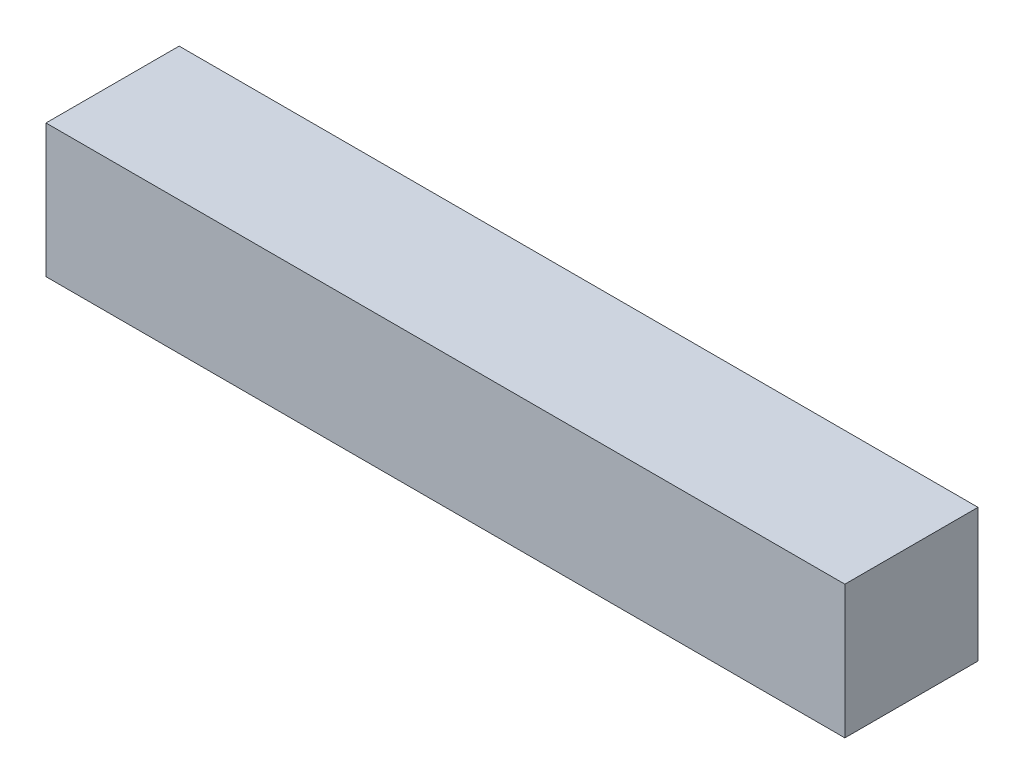
SolidWorks part; units mm, degrees
material "Plain Carbon Steel"
ref_plane "Front" through (0, 0, 0) normal (0, 0, 1) x (1, 0, 0)
ref_plane "Top" through (0, 0, 0) normal (0, 1, 0) x (1, 0, 0)
ref_plane "Right" through (0, 0, 0) normal (1, 0, 0) x (0, 0, -1)
sketch "Sketch1" plane through (0, 0, 0) normal (1, 0, 0) x (0, 0, -1)
  line L1 (0, 0) -> (25.4, 0)
  line L2 (0, 0) -> (0, 25.4)
  line L3 (0, 25.4) -> (25.4, 25.4)
  line L4 (25.4, 0) -> (25.4, 25.4)
  dimension "D1" = 25.4
  dimension "D2" = 25.4
extrude "Boss-Extrude1" add sketch "Sketch1" along normal blind 152.4
